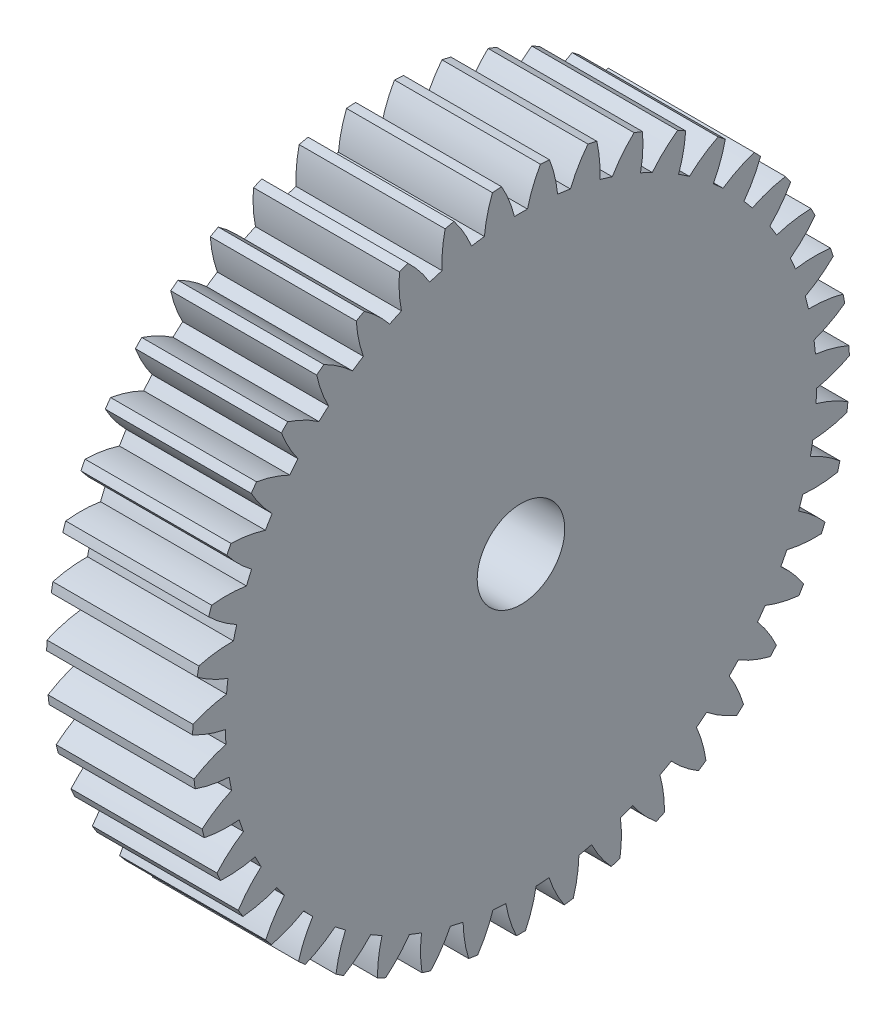
SolidWorks part; units mm, degrees
ref_plane "Plane1" through (0, 0, 0) normal (0, 0, 1) x (1, 0, 0)
ref_plane "Plane2" through (0, 0, 0) normal (0, 1, 0) x (1, 0, 0)
ref_plane "Plane3" through (0, 0, 0) normal (1, 0, 0) x (0, 0, -1)
other "Configuration Table"
sketch "HoldingSke" plane through (0, 0, 0) normal (0, 1, 0) x (1, 0, 0)
  line L0 (0, 0) -> (0.7314, -0.682)
  line L1 (-15, 0) -> (100, 0) construction
  line L2 (0, 0) -> (-2.1039, 2.3779)
  line L3 (0, 0) -> (-11.863, 4.5341)
  line L4 (0, 0) -> (6.316, 5.8897)
  line L5 (0, 0) -> (-46.8476, -17.4728)
  line L6 (0, 0) -> (-8.2896, -5.593)
  line L7 (-2.1039, 2.3779) -> (8.6586, 51.2059)
  line L8 (-76.2, 54.61) -> (-75.2, 54.61)
  line L9 (-71.009, 38.7566) -> (-53.1078, 45.2721)
  line L10 (-76.2, 71.12) -> (104.1128, 71.12)
  line L11 (0, 0) -> (-10, 0)
  line L12 (-76.2, 101.6) -> (-76.162, 101.6)
  line L13 (24.9733, 27.94) -> (52.9518, 28.4284)
  line L14 (24.9733, 27.94) -> (24.9743, 27.94)
  line L15 (24.9733, 27.94) -> (100.4006, 29.5858)
  line L16 (-63.627, -1) -> (-12.827, -1)
  circle A0 centre (0, 0) radius 3
  circle A1 centre (0, 0) radius 20.249
  circle A2 centre (0, 0) radius 37.5
  circle A3 centre (0, 0) radius 3
  dimension "MHD" = 40.498
  dimension "Hub_dia" = 75
  dimension "Bore" = 6
  dimension "MBD" = 6
  dimension "Num_teeth" = 43
  dimension "Pitch" = 1
  dimension "Overall_len" = 50
  dimension "Show_teeth" = 43
  dimension "Thickness" = 10
  dimension "OAL" = 50.0001
  dimension "T_dim" = 1
  dimension "Ap" = 20
  dimension "H" = 19.05
  dimension "Pitch_radius" = 180.3128
  dimension "Width" = 10
  dimension "Backlash" = 0.038
  dimension "Addendum_fac" = 1
  dimension "Dedendum_fac" = 1.25
  dimension "Clearance_fac" = 0.25
  dimension "Dedendum_add" = 0.001
  dimension "Module" = 1
sketch "BasProSke" plane through (0, 0, 0) normal (0, 1, 0) x (1, 0, 0)
  line L0 (-10, 0) -> (60, 0) construction
  line L1 (0, 0) -> (0, 22.5)
  line L2 (0, 0) -> (10, 0)
  line L3 (10, 0) -> (10, 22.5)
  line L4 (10, 22.5) -> (0, 22.5)
  dimension "Thickness" = 10
  dimension "Diameter" = 45
revolve "Base-Revolve" add sketch "BasProSke" angle 360 about L0
sketch "TooCutSke" plane through (0, 0, 0) normal (1, 0, 0) x (0, 0, -1)
  line L1 (0, 0) -> (0, 107) construction
  line L2 (0, 0) -> (-0.8517, 21.4831) construction
  line L3 (0, 0) -> (-3.137, 42.8613) construction
  line L4 (-0.8517, 21.4831) -> (-1.5685, 21.4307) construction
  arc A0 (0.4449, 20.2441) -> (-0.4449, 20.2441) centre (0, 0) ccw
  arc A1 (1.3459, 22.4852) -> (-1.3459, 22.4852) centre (0, 0) ccw
  circle A2 centre (0, 0) radius 21.5 construction
  circle A3 centre (0, 0) radius 20.2034 construction
  arc A4 (-0.4449, 20.2441) -> (-1.3459, 22.4852) centre (-8.7955, 18.1883) ccw
  arc A5 (1.3459, 22.4852) -> (0.4449, 20.2441) centre (8.7955, 18.1883) ccw
  dimension "Root_dia" = 40.498
  dimension "Overcut_dia" = 45.0508
  dimension "Pitch_dia" = 43
  dimension "Base_dia" = 40.4068
  dimension "Flank_rad" = 8.6
  dimension "Half_ang" = 4.186
  dimension "Half_CT" = 0.7187
extrude "ToothCut" cut sketch "TooCutSke" along normal through all
fillet "Breaks" [suppressed] radius 0.02
fillet "RootFillets" [suppressed] radius 0.251
pattern_circular "TeethCuts" count 43 every 8.372 about axis through (-10, 0, 0) along (1, 0, 0) of "ToothCut", "RootFillets", "Breaks"
sketch "HubNeaOneSke" plane through (0, 0, 0) normal (-1, 0, 0) x (0, 0, 1)
  circle A0 centre (0, 0) radius 20.249
  dimension "Diameter" = 40.498
extrude "HubNearOne" [suppressed] add sketch "HubNeaOneSke" along normal blind 40.0001
sketch "HubNeaBotSke" plane through (0, 0, 0) normal (-1, 0, 0) x (0, 0, 1)
  circle A0 centre (0, 0) radius 20.249
  dimension "Diameter" = 40.498
extrude "HubNearBoth" [suppressed] add sketch "HubNeaBotSke" along normal blind 20
ref_plane "FarPln" through (10, 0, 0) normal (1, 0, 0) x (0, 0, -1)
sketch "HubFarSke" plane through (10, 0, 0) normal (1, 0, 0) x (0, 0, -1)
  circle A0 centre (0, 0) radius 20.249
  dimension "Diameter" = 40.498
extrude "HubFar" [suppressed] add sketch "HubFarSke" along normal blind 20
sketch "BorSke" plane through (0, 0, 0) normal (1, 0, 0) x (0, 0, -1)
  circle A0 centre (0, 0) radius 3
  dimension "Diameter" = 6
extrude "Bore" cut sketch "BorSke" along normal mid plane 100.0001
sketch "KeySke" plane through (0, 0, 0) normal (1, 0, 0) x (0, 0, -1)
  line L0 (-1, 0) -> (-1, 4)
  line L1 (-1, 4) -> (1, 4)
  line L2 (1, 4) -> (1, 0)
  line L3 (0, 0) -> (0, 34) construction
  line L4 (-1, 0) -> (1, 0)
  dimension "Offset" = 4
  dimension "Width" = 2
extrude "Keyway" [suppressed] cut sketch "KeySke" along normal mid plane 100.0001
pattern_circular "Keyway2" [suppressed] count 2 every 90 about axis through (-10, 0, 0) along (1, 0, 0)
equation "' \"Module@HoldingSke\" = 6.35"
equation "' \"Num_teeth@HoldingSke\" = 12"
equation "' \"Ap@HoldingSke\" =  20"
equation "' \"Ap@HoldingSke\" = 20"
equation "' \"Width@HoldingSke\" = 0.5 * 25.4"
equation "' \"Hub_dia@HoldingSke\"= 1 * 25.4"
equation "' \"Hub_dia@HoldingSke\" = 1 * 25.4"
equation "' \"Overall_len@HoldingSke\" = 1.0 * 25.4"
equation "' \"Bore@HoldingSke\" = 0.75 * 25.4"
equation "' \"T_dim@HoldingSke\" = 0.1 * 25.4"
equation "' \"Width@KeySke\" = 0.25 * 25.4"
equation "' \"Show_teeth@HoldingSke\" = 13"
equation "' \"Backlash@HoldingSke\" = 0.009 * 25.4"
equation "' \"Addendum_fac@HoldingSke\" = 1.0"
equation "' \"Dedendum_fac@HoldingSke\" = 1.25"
equation "' \"Dedendum_add@HoldingSke\" = 0.00005 * 25.4"
equation "' \"Clearance_fac@HoldingSke\" = 0.25"
equation "\"Pitch@HoldingSke\" = 1 / \"Module@HoldingSke\""
equation "\"Overcut_dia@TooCutSke\" = (\"Num_teeth@HoldingSke\" + 2 * \"Addendum_fac@HoldingSke\") / \"Pitch@HoldingSke\" + 0.002 * 25.4"
equation "\"Pitch_dia@TooCutSke\" = \"Num_teeth@HoldingSke\" / \"Pitch@HoldingSke\""
equation "\"Base_dia@TooCutSke\" = \"Num_teeth@HoldingSke\" / \"Pitch@HoldingSke\" * cos((\"Ap@HoldingSke\"  * 3.14159265 / 180))"
equation "\"Root_dia@TooCutSke\" = (\"Num_teeth@HoldingSke\" + 2) / \"Pitch@HoldingSke\" - 2 * (\"Addendum_fac@HoldingSke\" + \"Dedendum_fac@HoldingSke\") / \"Pitch@HoldingSke\" - \"Dedendum_add@HoldingSke\" * 2"
equation "\"Half_ang@TooCutSke\" = 180 / \"Num_teeth@HoldingSke\""
equation "\"Half_CT@TooCutSke\" = \"Num_teeth@HoldingSke\" / \"Pitch@HoldingSke\" * sin((3.14159265 / 2 / \"Num_teeth@HoldingSke\")) / 2 - 7 * \"Backlash@HoldingSke\" / 4"
equation "\"Flank_rad@TooCutSke\" = \"Num_teeth@HoldingSke\" / \"Pitch@HoldingSke\" / 5"
equation "\"Radius@RootFillets\" = \"Clearance_fac@HoldingSke\" / \"Pitch@HoldingSke\" + \"Dedendum_add@HoldingSke\""
equation "\"Break_rad@Breaks\" = 0.02 / \"Pitch@HoldingSke\""
equation "\"Thickness@HoldingSke\" = \"Width@HoldingSke\""
equation "\"OAL@HoldingSke\" = \"Thickness@HoldingSke\""
equation "\"MHD@HoldingSke\" = (\"Num_teeth@HoldingSke\" + 2) / \"Pitch@HoldingSke\" - 2 * (\"Addendum_fac@HoldingSke\" + \"Dedendum_fac@HoldingSke\")  / \"Pitch@HoldingSke\" - \"Dedendum_add@HoldingSke\" * 2"
equation "\"MBD@HoldingSke\" = (\"Num_teeth@HoldingSke\" + 2) / \"Pitch@HoldingSke\" - 2 * (\"Addendum_fac@HoldingSke\" + \"Dedendum_fac@HoldingSke\")  / \"Pitch@HoldingSke\" - \"Dedendum_add@HoldingSke\" * 2 - 0.002 * 25.4"
equation "\"MHD@HoldingSke\" = ((sgn( \"MHD@HoldingSke\" - \"Hub_dia@HoldingSke\" )-1)*( \"MHD@HoldingSke\" - \"Hub_dia@HoldingSke\" ))/-2+ \"Hub_dia@HoldingSke\""
equation "\"MBD@HoldingSke\" = ((sgn( \"MBD@HoldingSke\" - \"Bore@HoldingSke\" )-1)*( \"MBD@HoldingSke\" - \"Bore@HoldingSke\" ))/-2+ \"Bore@HoldingSke\""
equation "\"OAL@HoldingSke\" = ((sgn( \"OAL@HoldingSke\" - \"Overall_len@HoldingSke\" )+1)*( \"OAL@HoldingSke\" - \"Overall_len@HoldingSke\" ))/2 + \"Overall_len@HoldingSke\" + 0.000002 * 25.4"
equation "\"Num_teeth@TeethCuts\" = int( \"Show_teeth@HoldingSke\" ) + 1"
equation "\"Num_teeth@TeethCuts\" = ((sgn( \"Num_teeth@TeethCuts\" - \"Num_teeth@HoldingSke\" )-1)*( \"Num_teeth@TeethCuts\" - \"Num_teeth@HoldingSke\" ))/-2+ \"Num_teeth@HoldingSke\""
equation "\"Num_teeth@TeethCuts\" = ((sgn( \"Num_teeth@TeethCuts\" - 2.0)+1)*( \"Num_teeth@TeethCuts\" - 2.0))/2 +2.0"
equation "\"Angle@TeethCuts\" = 360.0 / \"Num_teeth@HoldingSke\""
equation "\"Diameter@BasProSke\" = (\"Num_teeth@HoldingSke\" + 2 * \"Addendum_fac@HoldingSke\") / \"Pitch@HoldingSke\""
equation "\"Thickness@BasProSke\"  = \"Thickness@HoldingSke\""
equation "' \"Fillet_rad@BasProSke\" =  \"Thickness@HoldingSke\" * 0.05"
equation "' \"Fillet_rad@BasProSke\" = \"Thickness@HoldingSke\" * 0.05"
equation "\"MHD@HoldingSke\" = ((sgn( \"MHD@HoldingSke\" - \"Root_dia@TooCutSke\" )-1)*( \"MHD@HoldingSke\" - \"Root_dia@TooCutSke\" ))/-2+ \"Root_dia@TooCutSke\""
equation "\"Diameter@HubNeaOneSke\" = \"MHD@HoldingSke\""
equation "\"Length@HubNearOne\" = \"OAL@HoldingSke\" - \"Thickness@BasProSke\""
equation "\"Diameter@HubNeaBotSke\" = \"MHD@HoldingSke\""
equation "\"Length@HubNearBoth\" = ( \"OAL@HoldingSke\" - \"Thickness@BasProSke\" ) / 2.0"
equation "\"Thickness@FarPln\" = \"Thickness@BasProSke\""
equation "\"Diameter@HubFarSke\" = \"MHD@HoldingSke\""
equation "\"Length@HubFar\" = ( \"OAL@HoldingSke\" - \"Thickness@BasProSke\" ) / 2.0"
equation "\"Diameter@BorSke\" = \"MBD@HoldingSke\""
equation "\"D1@Bore\" = \"OAL@HoldingSke\" * 2.0"
equation "\"D1@Keyway\" = \"OAL@HoldingSke\" * 2.0"
equation "\"Offset@KeySke\" = \"T_dim@HoldingSke\" + \"MBD@HoldingSke\" / 2.0"
